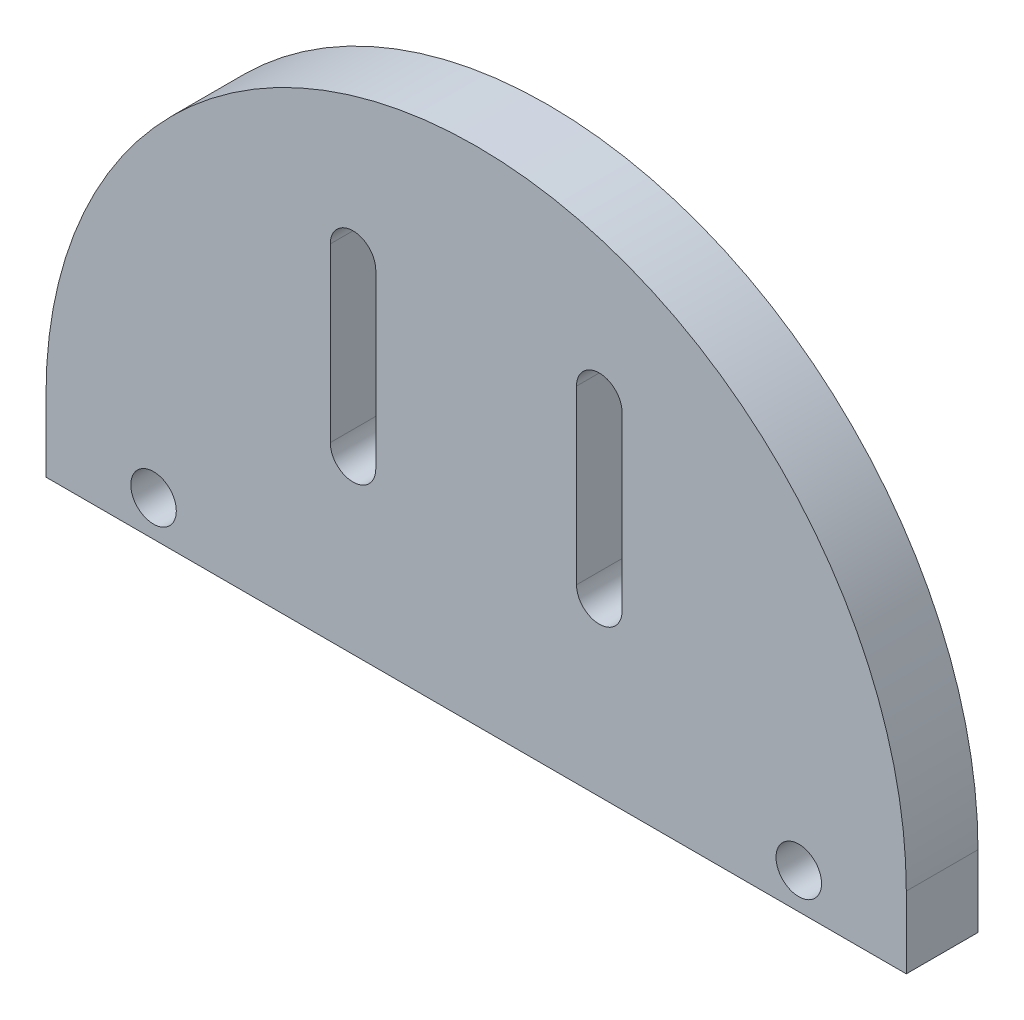
SolidWorks part; units mm, degrees
material "Pino"
ref_plane "Alzado" through (0, 0, 0) normal (0, 0, 1) x (1, 0, 0)
ref_plane "Planta" through (0, 0, 0) normal (0, 1, 0) x (1, 0, 0)
ref_plane "Vista lateral" through (0, 0, 0) normal (1, 0, 0) x (0, 0, -1)
sketch "Croquis1" plane through (0, 0, 0) normal (0, 0, 1) x (1, 0, 0)
  line L0 (-30, 0) -> (30, 0) construction
  line L1 (-30, 0) -> (-30, -5)
  line L2 (-30, -5) -> (30, -5)
  line L3 (30, -5) -> (30, 0)
  line L4 (0, 0) -> (0, 19.4879) construction
  line L5 (-10.175, 7) -> (-10.175, 19)
  line L6 (-7, 7) -> (-7, 19)
  line L7 (7, 7) -> (7, 19)
  line L8 (10.175, 7) -> (10.175, 19)
  line L9 (-22.5, -2.5) -> (22.5, -2.5) construction
  line L10 (0, 0) -> (0, -5) construction
  arc A0 (30, 0) -> (-30, 0) centre (0, 0) ccw
  arc A1 (-10.175, 7) -> (-7, 7) centre (-8.5875, 7) ccw
  arc A2 (-7, 19) -> (-10.175, 19) centre (-8.5875, 19) ccw
  arc A3 (7, 19) -> (10.175, 19) centre (8.5875, 19) cw
  arc A4 (10.175, 7) -> (7, 7) centre (8.5875, 7) cw
  circle A5 centre (-22.5, -2.5) radius 1.5875
  circle A6 centre (22.5, -2.5) radius 1.5875
  point P23 (0, -2.5)
  dimension "D1" = 30
  dimension "D3" = 1.5875
  dimension "D5" = 7
  dimension "D2" = 5
  dimension "D4" = 12
  dimension "D6" = 7
  dimension "D7" = 45
extrude "Saliente-Extruir1" add sketch "Croquis1" along normal blind 5
